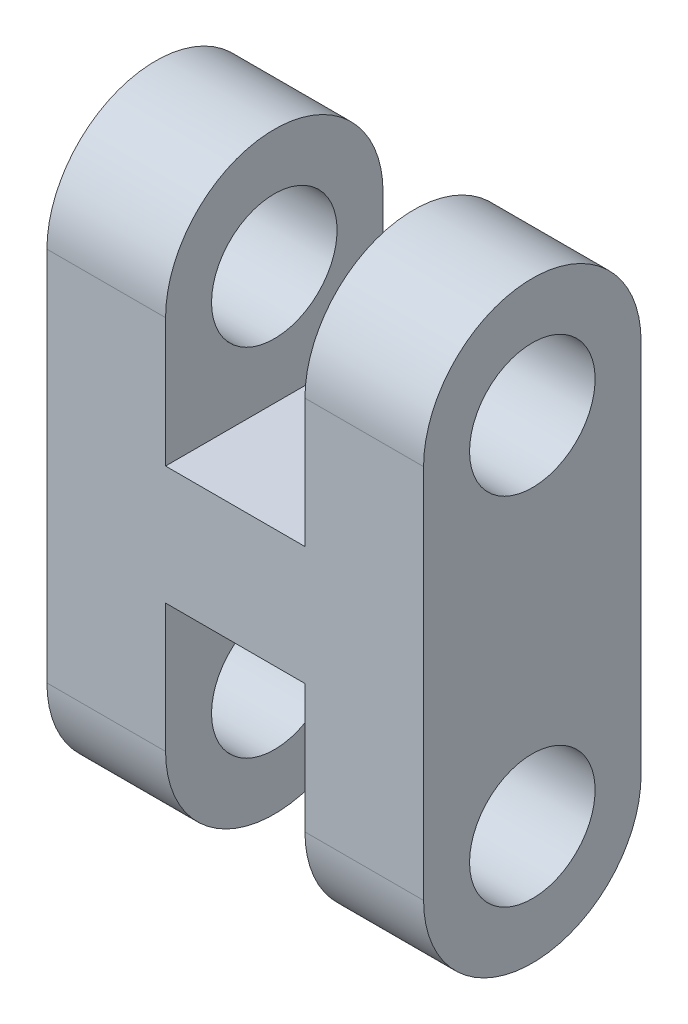
SolidWorks part; units mm, degrees
material "ABS"
ref_plane "Front Plane" through (0, 0, 0) normal (0, 0, 1) x (1, 0, 0)
ref_plane "Top Plane" through (0, 0, 0) normal (0, 1, 0) x (1, 0, 0)
ref_plane "Right Plane" through (0, 0, 0) normal (1, 0, 0) x (0, 0, -1)
sketch "Sketch1" plane through (0, 0, 0) normal (0, 0, 1) x (1, 0, 0)
  line L0 (0, 0) -> (3.525, 0) construction
  line L1 (0, 0) -> (-3, 0)
  line L2 (0, 0) -> (0, 6)
  line L4 (3.525, 0) -> (3.525, 6)
  line L5 (3.525, 0) -> (6.525, 0)
  line L6 (6.525, 0) -> (6.525, 15)
  line L7 (-3, 0) -> (-3, 15)
  line L8 (-3, 7.5) -> (6.525, 7.5) construction
  line L9 (3.525, 15) -> (6.525, 15)
  line L10 (3.525, 9) -> (3.525, 15)
  line L11 (0, 9) -> (3.525, 9)
  line L12 (0, 15) -> (-3, 15)
  line L13 (0, 15) -> (0, 9)
  line L15 (0, 6) -> (3.525, 6)
  dimension "D1" = 15
  dimension "D2" = 1.5
  dimension "D3" = 9.525
  dimension "D4" = 3
extrude "Boss-Extrude1" add sketch "Sketch1" along normal blind 5.5
sketch "Sketch3" plane through (-3, 0, 0) normal (-1, 0, 0) x (0, 0, 1)
  line L0 (2.75, 9) -> (2.75, 15) construction
  line L1 (5.5, 9) -> (0, 9) construction
  line L2 (5.5, 15) -> (0, 15) construction
  line L3 (2.75, 12) -> (5.5, 12) construction
  line L4 (5.5, 15) -> (5.5, 0) construction
  line L5 (0, 15) -> (0, 0) construction
  line L6 (0, 12.25) -> (0, 15)
  line L7 (0, 15) -> (2.75, 15)
  line L8 (5.5, 12.25) -> (5.5, 15)
  line L9 (5.5, 15) -> (2.75, 15)
  line L10 (0, 7.5) -> (5.5, 7.5) construction
  line L11 (0, 0) -> (2.75, 0)
  line L12 (5.5, 0) -> (2.75, 0)
  line L13 (5.5, 2.75) -> (5.5, 0)
  line L14 (0, 2.75) -> (0, 0)
  circle A0 centre (2.75, 12) radius 1.5875
  arc A1 (2.75, 15) -> (0, 12.25) centre (2.75, 12.25) ccw
  arc A2 (2.75, 15) -> (5.5, 12.25) centre (2.75, 12.25) cw
  arc A3 (2.75, 0) -> (5.5, 2.75) centre (2.75, 2.75) ccw
  arc A4 (2.75, 0) -> (0, 2.75) centre (2.75, 2.75) cw
  circle A5 centre (2.75, 3) radius 1.5875
  line M1 (0, 15) -> (0, 0)
  line M2 (0, 0) -> (5.5, 0)
  line M3 (5.5, 0) -> (5.5, 15)
  line M4 (5.5, 15) -> (0, 15)
extrude "Cut-Extrude1" cut sketch "Sketch3" against normal up to surface (9.525 mm away) contours A2 M4 M3 | A1 M4 M1 | A0 | A5 | A4 M2 M1 | A3 L13 L12 up to face at (6.525, 7.5, 2.75)
